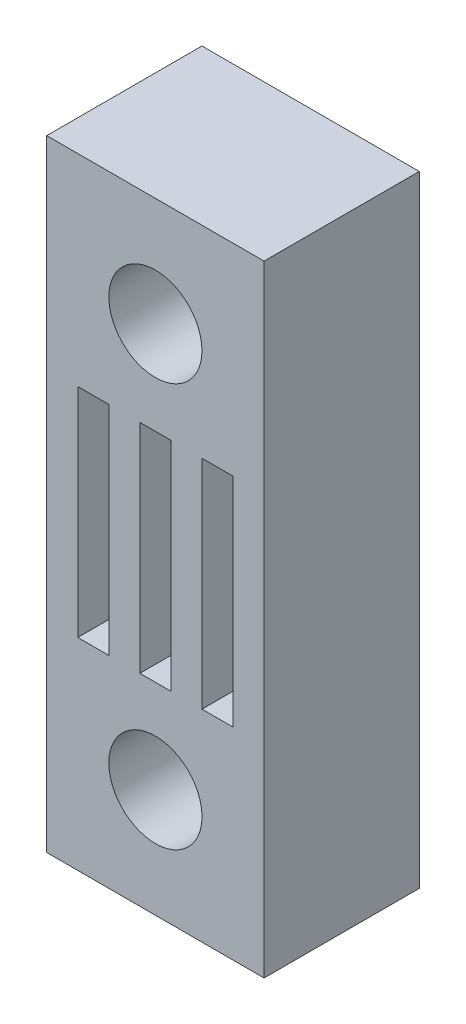
SolidWorks part; units mm, degrees
material "Acrylic (Medium-high impact)"
ref_plane "Front Plane" through (0, 0, 0) normal (0, 0, 1) x (1, 0, 0)
ref_plane "Top Plane" through (0, 0, 0) normal (0, 1, 0) x (1, 0, 0)
ref_plane "Right Plane" through (0, 0, 0) normal (1, 0, 0) x (0, 0, -1)
sketch "Sketch1" plane through (0, 0, 0) normal (0, 0, 1) x (1, 0, 0)
  line L0 (0, 10) -> (7, 10) construction
  line L1 (0, 0) -> (7, 0)
  line L2 (0, 0) -> (0, 20)
  line L3 (0, 20) -> (7, 20)
  line L4 (7, 0) -> (7, 20)
  line L5 (1, 6.5) -> (1, 13.5)
  line L6 (1, 13.5) -> (2, 13.5)
  line L7 (2, 13.5) -> (2, 6.5)
  line L8 (3, 6.5) -> (3, 13.5)
  line L9 (3, 13.5) -> (4, 13.5)
  line L10 (4, 13.5) -> (4, 6.5)
  line L11 (5, 6.5) -> (5, 13.5)
  line L12 (5, 13.5) -> (6, 13.5)
  line L13 (6, 13.5) -> (6, 6.5)
  line L14 (5, 6.5) -> (6, 6.5)
  line L15 (3, 6.5) -> (4, 6.5)
  line L16 (1, 6.5) -> (2, 6.5)
  line L17 (3.5, 20) -> (3.5, 0) construction
  circle A0 centre (3.5, 16.5) radius 1.5
  circle A1 centre (3.5, 3.5) radius 1.5
  point P24 (6, 10)
  point P25 (5, 10)
  point P26 (4, 10)
  point P27 (3, 10)
  point P28 (2, 10)
  point P29 (1, 10)
  dimension "D3" = 3
  dimension "D1" = 20
  dimension "D2" = 7
  dimension "D4" = 6.5
  dimension "D5" = 3.5
  dimension "D6" = 1
  dimension "D7" = 1
  dimension "D8" = 3
extrude "Boss-Extrude1" add sketch "Sketch1" along normal blind 5
